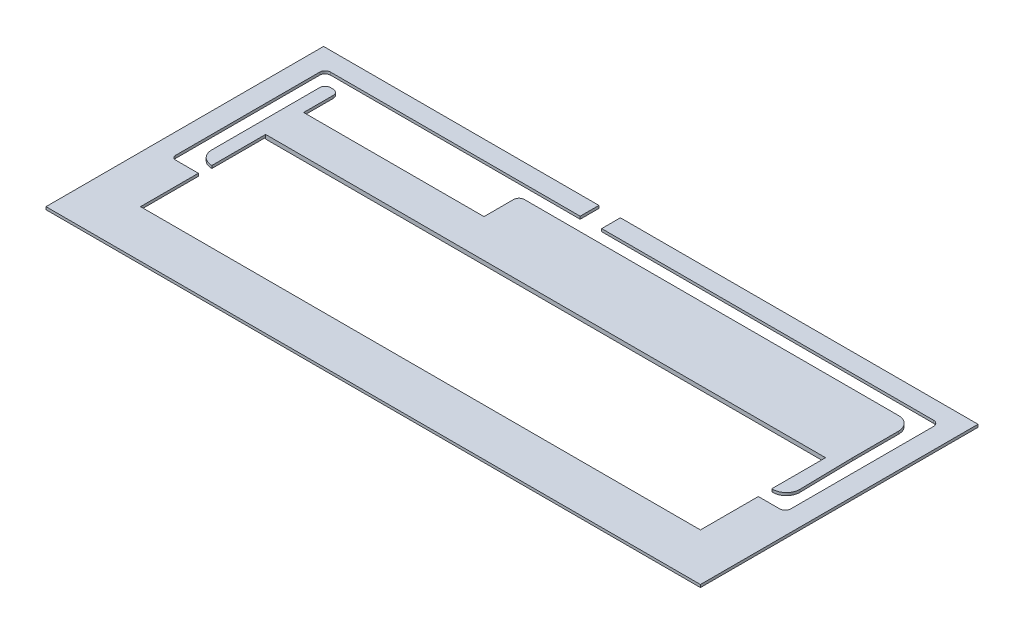
SolidWorks part; units mm, degrees
other "Marca1"
sketch "Croquis6" plane through (483.1, 12, 3.1) normal (0.4175, 0.3737, 0.8283) x (0.8528, 0.1536, -0.4991)
material "Balsa"
ref_plane "Alzado" through (0, 0, 0) normal (0, 0, 1) x (1, 0, 0)
ref_plane "Planta" through (0, 0, 0) normal (0, 1, 0) x (1, 0, 0)
ref_plane "Vista lateral" through (0, 0, 0) normal (1, 0, 0) x (0, 0, -1)
sketch "Croquis1" plane through (0, 0, 0) normal (0, 1, 0) x (1, 0, 0)
  line L0 (0, 0) -> (-3.1, 0) construction
  line L1 (0, 0) -> (480, 0)
  line L2 (0, 0) -> (0, 200)
  line L3 (0, 200) -> (480, 200)
  line L4 (480, 0) -> (480, 200)
  line L5 (0, 0) -> (0, -3.1) construction
  line L6 (-3.1, 0) -> (-3.1, -3.1) construction
  line L7 (-3.1, -3.1) -> (0, -3.1) construction
  line L8 (480, 200) -> (480, 203.1) construction
  line L9 (480, 203.1) -> (483.1, 203.1) construction
  line L11 (-3.1, -3.1) -> (483.1, -3.1)
  line L12 (-3.1, -3.1) -> (-3.1, 203.1)
  line L13 (-3.1, 203.1) -> (483.1, 203.1)
  line L14 (483.1, -3.1) -> (483.1, 203.1)
extrude "Saliente-Extruir1" add sketch "Croquis1" along normal blind 12 contours L1 L4 L3 L2 | L11 L14 L13 L12 L4 L1 L2 L3
sketch "Croquis2" plane through (0, 12, 0) normal (0, 1, 0) x (1, 0, 0)
  line L0 (21.9636, 184.1902) -> (21.9636, 179.1902) construction
  line L1 (17, 184.1902) -> (17, 189.1902) construction
  line L2 (17, 189.1902) -> (16, 189.1902)
  line L3 (28, 184.1902) -> (58, 184.1902) construction
  line L4 (32, 128) -> (448, 128)
  line L6 (32, 32) -> (448, 32)
  line L8 (32, 128) -> (448, 32) construction
  line L9 (32, 32) -> (448, 128) construction
  line L10 (32, 80) -> (17, 80) construction
  line L15 (17, 184.1902) -> (12, 184.1902) construction
  line L16 (28, 184.1902) -> (17, 184.1902) construction
  line L17 (17, 184.1902) -> (17, 80) construction
  line L18 (17, 184.1902) -> (17, 149.1902) construction
  line L19 (12, 185.1902) -> (12, 184.1902)
  line L20 (12, 146.1902) -> (12, 184.1902)
  line L21 (463, 189.1902) -> (464, 189.1902)
  line L22 (17, 80) -> (12, 80) construction
  line L23 (17, 80) -> (17, 75) construction
  line L24 (12, 184.1902) -> (12, 80)
  line L25 (12, 80) -> (12, 78)
  line L26 (15, 75) -> (17, 75)
  line L27 (17, 75) -> (32, 75)
  line L28 (17, 80) -> (21.9636, 80) construction
  line L29 (468, 185.1902) -> (468, 79)
  line L30 (31.9636, 85) -> (32, 85)
  line L31 (463, 189.1902) -> (448, 189.1902)
  line L32 (21.9636, 95) -> (21.9636, 175.1902)
  line L33 (25.9636, 179.1902) -> (28, 179.1902)
  line L34 (58, 184.1902) -> (448, 184.1902) construction
  line L35 (448, 80) -> (463, 80) construction
  line L36 (463, 80) -> (463, 184.1902) construction
  line L37 (463, 184.1902) -> (448, 184.1902) construction
  line L38 (459, 75) -> (459, 85) construction
  line L39 (448.8054, 85) -> (448, 85)
  line L40 (459, 75) -> (448, 75)
  line L41 (458.8036, 95.1927) -> (458.0364, 135)
  line L42 (32, 179.1902) -> (32, 189.1902) construction
  line L43 (448.0364, 125) -> (448, 125)
  line L44 (32, 189.1902) -> (17, 189.1902)
  line L45 (458.0364, 135) -> (458.0364, 169.1902)
  line L46 (464, 75) -> (459, 75)
  line L47 (166, 189.1902) -> (448, 189.1902)
  line L48 (32, 189.1902) -> (166, 189.1902)
  line L50 (32, 153.1902) -> (166, 153.1902)
  line L52 (448.0364, 179.1902) -> (170, 179.1902)
  line L53 (166, 175.1902) -> (166, 153.1902)
  line L54 (32, 175.1902) -> (32, 153.1902)
  line L55 (32, 128) -> (32, 85)
  line L56 (32, 75) -> (32, 32)
  line L57 (32, 85) -> (32, 75)
  line L58 (448, 128) -> (448, 85)
  line L59 (448, 32) -> (448, 75)
  line L60 (448, 85) -> (448, 75)
  line L61 (201.4487, 189.1902) -> (201.4487, 203.1)
  line L62 (-3.1, 203.1) -> (483.1, 203.1) construction
  line L63 (201.4487, 203.1) -> (217.4247, 203.1)
  line L64 (217.4247, 203.1) -> (217.4247, 189.1902)
  arc A0 (458.8036, 95.1927) -> (448.8054, 85) centre (448.8054, 95) cw
  arc A1 (458.0364, 169.1902) -> (448.0364, 179.1902) centre (448.0364, 169.1902) ccw
  arc A2 (21.9636, 95) -> (31.9636, 85) centre (31.9636, 95) ccw
  arc A3 (16, 189.1902) -> (12, 185.1902) centre (16, 185.1902) ccw
  arc A4 (464, 189.1902) -> (468, 185.1902) centre (464, 185.1902) cw
  arc A5 (468, 79) -> (464, 75) centre (464, 79) cw
  arc A6 (170, 179.1902) -> (166, 175.1902) centre (170, 175.1902) ccw
  arc A7 (12, 78) -> (15, 75) centre (15, 78) ccw
  arc A8 (21.9636, 175.1902) -> (25.9636, 179.1902) centre (25.9636, 175.1902) cw
  arc A9 (28, 179.1902) -> (32, 175.1902) centre (28, 175.1902) cw
  point P6 (240, 80)
  dimension "D1" = 10
  dimension "D2" = 4
  dimension "D3" = 4
sketch "Croquis3" plane through (0, 12, 0) normal (0, 1, 0) x (1, 0, 0)
  line L1 (0, 0) -> (480, 0)
  line L2 (0, 0) -> (0, 200)
  line L3 (0, 200) -> (480, 200)
  line L4 (480, 0) -> (480, 200)
  line L5 (-3.1, -3.1) -> (483.1, -3.1)
  line L6 (-3.1, -3.1) -> (-3.1, 203.1)
  line L7 (-3.1, 203.1) -> (483.1, 203.1)
  line L8 (483.1, -3.1) -> (483.1, 203.1)
extrude "Cortar-Extruir1" cut sketch "Croquis3" against normal blind 5
extrude "Cortar-Extruir3" cut sketch "Croquis2" against normal blind 8
sketch "Croquis4" plane through (0, 12, 0) normal (0, 1, 0) x (1, 0, 0)
  line L0 (32, 128) -> (32, 134)
  line L1 (32, 134) -> (52, 134)
  line L2 (52, 134) -> (52, 128)
  line L3 (32, 128) -> (448, 128) construction
  line L4 (52, 128) -> (32, 128)
  line L5 (240, 32) -> (240, 128) construction
  line L6 (32, 32) -> (448, 32) construction
  line L7 (32, 128) -> (448, 128) construction
  line L8 (240, 80) -> (282.8706, 80) construction
  line L9 (428, 134) -> (428, 128)
  line L10 (448, 128) -> (448, 134)
  line L11 (428, 128) -> (448, 128)
  line L12 (448, 134) -> (428, 134)
  line L13 (448, 32) -> (448, 26)
  line L14 (428, 32) -> (448, 32)
  line L15 (448, 26) -> (428, 26)
  line L16 (428, 26) -> (428, 32)
  line L17 (52, 26) -> (52, 32)
  line L18 (52, 32) -> (32, 32)
  line L19 (32, 26) -> (52, 26)
  line L20 (32, 32) -> (32, 26)
  line L21 (32, 75) -> (32, 69)
  line L22 (32, 75) -> (32, 32) construction
  line L23 (12, 80) -> (6, 80) construction
  line L24 (12, 185.1902) -> (12, 78) construction
  line L25 (32, 69) -> (6, 69)
  line L26 (16, 189.1902) -> (16, 195.1902) construction
  line L27 (6, 69) -> (6, 80)
  line L28 (6, 80) -> (6, 195.1902)
  line L29 (6, 195.1902) -> (16, 195.1902)
  line L30 (32, 189.1902) -> (32, 195.1902)
  line L31 (16, 189.1902) -> (201.4487, 189.1902) construction
  line L32 (32, 195.1902) -> (16, 195.1902)
  line L33 (16, 189.1902) -> (32, 189.1902)
  line L34 (12, 185.1902) -> (12, 80)
  line L35 (32, 75) -> (15, 75)
  line L36 (12, 80) -> (12, 78)
  line L37 (31.9636, 85) -> (32, 128)
  line L38 (32, 175.1902) -> (32, 134)
  line L39 (25.9636, 179.1902) -> (28, 179.1902)
  line L40 (21.9636, 175.1902) -> (21.9636, 95)
  line L41 (99, 153.1902) -> (99, 189.1902) construction
  line L42 (32, 153.1902) -> (52, 153.1902)
  line L43 (32, 153.1902) -> (32, 147.1902)
  line L44 (32, 147.1902) -> (52, 147.1902)
  line L45 (52, 153.1902) -> (52, 147.1902)
  line L46 (32, 153.1902) -> (166, 153.1902) construction
  line L47 (99, 171.1902) -> (116.5825, 171.1902) construction
  line L48 (52, 189.1902) -> (52, 195.1902)
  line L49 (32, 195.1902) -> (52, 195.1902)
  line L50 (32, 189.1902) -> (52, 189.1902)
  line L51 (146, 189.1902) -> (146, 195.1902)
  line L52 (166, 189.1902) -> (146, 189.1902)
  line L53 (166, 195.1902) -> (146, 195.1902)
  line L54 (166, 189.1902) -> (166, 195.1902)
  line L55 (166, 153.1902) -> (146, 153.1902)
  line L56 (166, 153.1902) -> (166, 147.1902)
  line L57 (146, 153.1902) -> (146, 147.1902)
  line L58 (166, 147.1902) -> (146, 147.1902)
  line L59 (468, 185.1902) -> (474, 185.1902) construction
  line L60 (464, 189.1902) -> (464, 195.1902) construction
  line L61 (464, 195.1902) -> (474, 195.1902) construction
  line L62 (166, 147.1902) -> (474, 147.1902) construction
  line L63 (448, 75) -> (448, 69) construction
  line L64 (166, 195.1902) -> (474, 195.1902)
  line L65 (166, 195.1902) -> (166, 147.1902)
  line L66 (166, 147.1902) -> (474, 147.1902)
  line L67 (474, 195.1902) -> (474, 147.1902)
  line L68 (448, 75) -> (448, 32) construction
  line L70 (474, 147.1902) -> (448, 147.1902)
  line L71 (474, 147.1902) -> (474, 69)
  line L72 (474, 69) -> (448, 69)
  line L73 (448, 147.1902) -> (448, 69)
  arc A0 (16, 189.1902) -> (12, 185.1902) centre (16, 185.1902) ccw
  arc A1 (12, 78) -> (15, 75) centre (15, 78) ccw
  arc A2 (21.9636, 95) -> (31.9636, 85) centre (31.9636, 95) ccw construction
  arc A3 (28, 179.1902) -> (32, 175.1902) centre (28, 175.1902) cw
  arc A4 (21.9636, 175.1902) -> (25.9636, 179.1902) centre (25.9636, 175.1902) cw
  arc A5 (21.9636, 95) -> (31.9636, 85) centre (31.9636, 95) ccw
  line M14 (32, 128) -> (448, 128)
  line M15 (448, 128) -> (448, 85)
  line M16 (448, 85) -> (448.8054, 85)
  arc M17 (448.8054, 85) -> (458.8036, 95.1927) centre (448.8054, 95) ccw
  line M18 (458.8036, 95.1927) -> (458.0364, 135)
  line M19 (458.0364, 135) -> (458.0364, 169.1902)
  arc M20 (458.0364, 169.1902) -> (448.0364, 179.1902) centre (448.0364, 169.1902) ccw
  line M21 (448.0364, 179.1902) -> (170, 179.1902)
  arc M22 (170, 179.1902) -> (166, 175.1902) centre (170, 175.1902) ccw
  line M23 (166, 175.1902) -> (166, 153.1902)
  line M24 (166, 153.1902) -> (32, 153.1902)
  line M25 (32, 153.1902) -> (32, 175.1902)
  arc M26 (32, 175.1902) -> (28, 179.1902) centre (28, 175.1902) ccw
  line M27 (28, 179.1902) -> (25.9636, 179.1902)
  arc M28 (25.9636, 179.1902) -> (21.9636, 175.1902) centre (25.9636, 175.1902) ccw
  line M29 (21.9636, 175.1902) -> (21.9636, 95)
  arc M30 (21.9636, 95) -> (31.9636, 85) centre (31.9636, 95) ccw
extrude "Cortar-Extruir4" cut sketch "Croquis4" against normal blind 3 contours L38 L37 L0 M25 M26 M27 M28 M29 M30 | L2 L1 L0 M14 | L45 L38 L44 M24 | A1 L36 L34 A0 L33 L30 L32 L29 L28 L27 L25 L21 L35 | L30 L50 L48 L49 | L18 L20 L19 L17 | L52 L54 L53 L51 | L58 L56 L57 M24 | L56 L66 M19 M20 M21 M22 M23 | L67 L64 L54 L65 L66 M22 M21 M20 M19 | L73 L72 L71 L66 M16 M19 M18 M17 | L10 L12 L9 M14 | L16 L15 L13 L14 | L66 L73 L10 M15 M16 M17 M18 M19
sketch "Croquis5" plane through (0, 4, 0) normal (0, 1, 0) x (1, 0, 0)
  line L0 (32.046, 84.9265) -> (32, 75)
  line L2 (32, 75) -> (15, 75)
  line L3 (25.9636, 179.1902) -> (28, 179.1902)
  line L4 (21.9636, 175.1902) -> (21.9636, 95)
  line L5 (32, 175.1902) -> (32, 153.1902)
  line L6 (32, 153.1902) -> (166, 153.1902)
  line L7 (166, 153.1902) -> (166, 175.1902)
  line L8 (170, 179.1902) -> (448.0364, 179.1902)
  line L9 (458.0364, 169.1902) -> (458.8036, 95.1927)
  line L10 (448.8054, 85) -> (448, 85)
  line L11 (448, 85) -> (448, 75)
  line L12 (448, 75) -> (464, 75)
  line L13 (468, 79) -> (468, 185.1902)
  line L14 (468, 185.1902) -> (468, 79) construction
  line L15 (464, 189.1902) -> (217.4247, 189.1902)
  line L16 (217.4247, 189.1902) -> (217.4247, 203.1)
  line L17 (217.4247, 203.1) -> (201.4487, 203.1)
  line L18 (201.4487, 203.1) -> (201.4487, 189.1902)
  line L19 (201.4487, 189.1902) -> (16, 189.1902)
  line L20 (12, 185.1902) -> (12, 78)
  arc A1 (12, 78) -> (15, 75) centre (15, 78) ccw
  arc A2 (25.9636, 179.1902) -> (21.9636, 175.1902) centre (25.9636, 175.1902) ccw
  arc A3 (21.9636, 95) -> (32.046, 84.9265) centre (32.0371, 95) ccw
  arc A4 (28, 179.1902) -> (32, 175.1902) centre (28, 175.1902) cw
  arc A5 (166, 175.1902) -> (170, 179.1902) centre (170, 175.1902) cw
  arc A6 (448.0364, 179.1902) -> (458.0364, 169.1902) centre (448.0364, 169.1902) cw
  arc A7 (448.8054, 85) -> (458.8036, 95.1927) centre (448.7156, 95.0881) ccw
  arc A8 (468, 79) -> (464, 75) centre (464, 79) cw
  arc A9 (468, 185.1902) -> (464, 189.1902) centre (464, 185.1902) ccw construction
  arc A10 (464, 189.1902) -> (468, 185.1902) centre (464, 185.1902) cw
  arc A11 (16, 189.1902) -> (12, 185.1902) centre (16, 185.1902) ccw
extrude "Cortar-Extruir5" cut sketch "Croquis5" against normal blind 2
sketch "Croquis7" plane through (0, 2, 0) normal (0, 1, 0) x (1, 0, 0)
  line L1 (-211.6054, 341.1803) -> (510.3417, 341.1803)
  line L2 (-211.6054, 341.1803) -> (-211.6054, -18.2396)
  line L3 (-211.6054, -18.2396) -> (510.3417, -18.2396)
  line L4 (510.3417, 341.1803) -> (510.3417, -18.2396)
  line L5 (-211.6054, 341.1803) -> (510.3417, -18.2396) construction
  line L6 (-211.6054, -18.2396) -> (510.3417, 341.1803) construction
  point P0 (149.3682, 161.4704)
extrude "Cortar-Extruir6" cut sketch "Croquis7" against normal blind 10
sketch "Croquis8" plane through (0, 4, 0) normal (0, 1, 0) x (1, 0, 0)
  line L1 (32, 128) -> (448, 128)
  line L2 (32, 128) -> (32, 32)
  line L3 (32, 32) -> (448, 32)
  line L4 (448, 128) -> (448, 32)
extrude "Cortar-Extruir7" cut sketch "Croquis8" against normal blind 10
sketch "Croquis9" plane through (0, 9, 0) normal (0, 1, 0) x (1, 0, 0)
  line L1 (512.9567, 229.5955) -> (-18.948, 229.5955)
  line L2 (512.9567, 229.5955) -> (512.9567, -16.7579)
  line L3 (512.9567, -16.7579) -> (-18.948, -16.7579)
  line L4 (-18.948, 229.5955) -> (-18.948, -16.7579)
sketch "Croquis10" plane through (0, 7, 0) normal (0, 1, 0) x (1, 0, 0)
  line L1 (-18.948, 229.5955) -> (512.9567, 229.5955)
  line L2 (-18.948, 229.5955) -> (-18.948, -16.7579)
  line L3 (-18.948, -16.7579) -> (512.9567, -16.7579)
  line L4 (512.9567, 229.5955) -> (512.9567, -16.7579)
ref_plane "Plano1" through (0, 5, 0) normal (0, -1, 0) x (-1, 0, 0)
sketch "Croquis11" plane through (0, 5, 0) normal (0, -1, 0) x (-1, 0, 0)
  line L1 (-512.9567, 229.5955) -> (18.948, 229.5955)
  line L2 (-512.9567, 229.5955) -> (-512.9567, -16.7579)
  line L3 (-512.9567, -16.7579) -> (18.948, -16.7579)
  line L4 (18.948, 229.5955) -> (18.948, -16.7579)
extrude "Cortar-Extruir9" cut sketch "Croquis9" along normal blind 10
extrude "Cortar-Extruir10" cut sketch "Croquis10" along normal blind 10 contours L1 L4 L3 L2
extrude "Cortar-Extruir11" cut sketch "Croquis11" along normal blind 10
sketch "Croquis12" plane through (0, 7, 0) normal (0, 1, 0) x (1, 0, 0)
  line L0 (448, 85) -> (448, 128) construction
  line L1 (32, 128) -> (448, 128)
  line L2 (32, 128) -> (32, 124.9526)
  line L3 (32, 124.9526) -> (448, 124.9526)
  line L4 (448, 128) -> (448, 124.9526)
extrude "Saliente-Extruir2" add sketch "Croquis12" against normal blind 3
